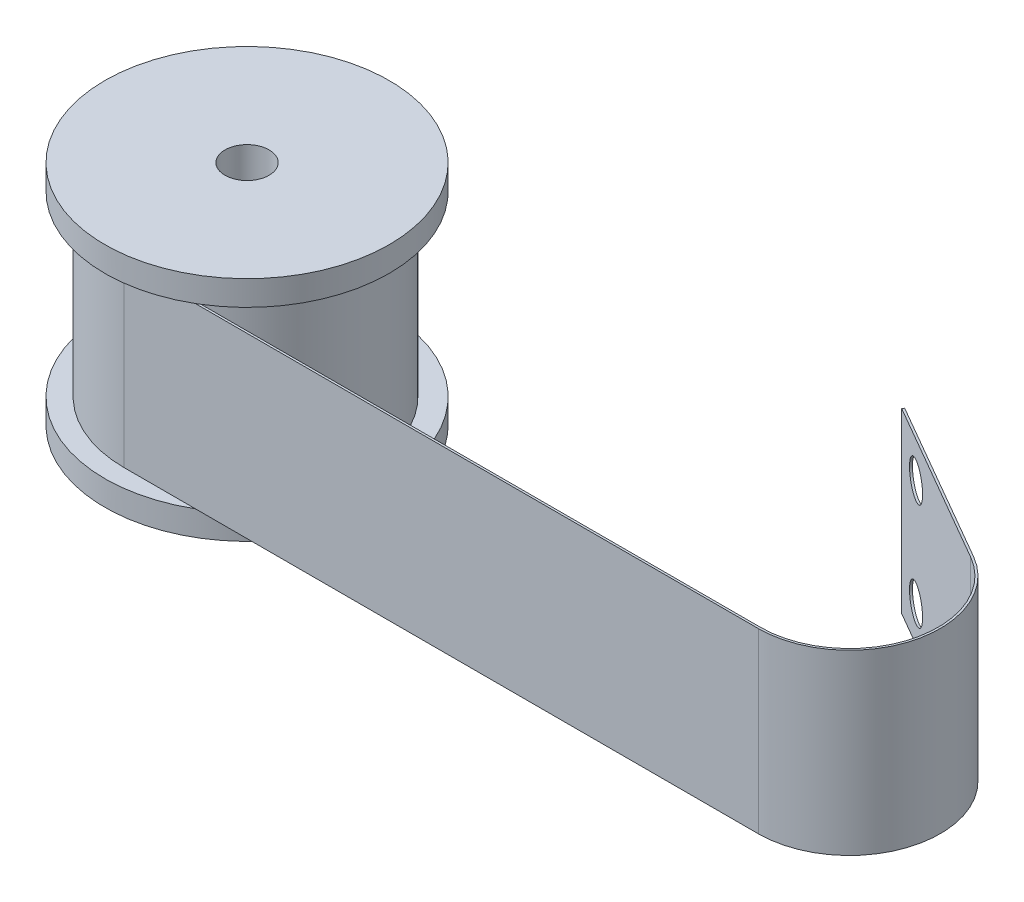
SolidWorks part; units mm, degrees
ref_plane "Front Plane" through (0, 0, 0) normal (0, 0, 1) x (1, 0, 0)
ref_plane "Top Plane" through (0, 0, 0) normal (0, 1, 0) x (1, 0, 0)
ref_plane "Right Plane" through (0, 0, 0) normal (1, 0, 0) x (0, 0, -1)
sketch "Sketch1" plane through (0, 0, 0) normal (0, 0, 1) x (1, 0, 0)
  line L0 (0, -1363.7477) -> (0, 66823.6351) construction
  line L1 (0, 16) -> (3.1, 16) construction
  line L2 (3.1, 0) -> (0, 0) construction
  line L3 (3.1, 16) -> (3.1, -16)
  line L4 (3.1, 0) -> (17, 0) construction
  line L5 (17, -12.5) -> (17, 12.5)
  line L6 (17, 12.5) -> (20, 12.5)
  line L7 (20, 12.5) -> (20, 16)
  line L8 (20, 16) -> (3.1, 16)
  line L9 (20, -12.5) -> (20, -16)
  line L10 (20, -16) -> (3.1, -16)
  line L11 (17, -12.5) -> (20, -12.5)
  dimension "D1" = 40
  dimension "D2" = 6.2
  dimension "D3" = 25
  dimension "D4" = 32
  dimension "D5" = 3
revolve "Revolve1" add sketch "Sketch1" angle 360 about L0
ref_plane "Plane1" through (0, 0, 17) normal (0, 0, 1) x (1, 0, 0)
sketch "Sketch2" plane through (0, -12.5, 0) normal (0, 1, 0) x (1, 0, 0)
  line L0 (0, -17) -> (89.2, -17)
  line L1 (95.45, 6.3253) -> (72.5003, 19.5753)
  line L2 (0, 17) -> (0, -17) construction
  circle A0 centre (0, 0) radius 17 construction
  arc A1 (89.2, -17) -> (95.45, 6.3253) centre (89.2, -4.5) ccw
  arc A2 (0, -17) -> (0, 17) centre (0, 0) cw
  point P6 (0, 0)
  dimension "D1" = 12.5
  dimension "D2" = 89.2
  dimension "D3" = 26.5
  dimension "D4" = 30
extrude "Extrude-Thin2" add sketch "Sketch2" along normal up to surface (25 mm away) thin
sketch "Sketch4" plane through (26.7514, 0, -46.3349) normal (0.5, 0, -0.866) x (-0.866, 0, -0.5)
  line L0 (-58.4995, 12.5) -> (-58.4995, -12.5) construction
  line L1 (-52.9995, 12.5) -> (-79.4995, 12.5) construction
  line L2 (-79.4995, -12.5) -> (-52.9995, -12.5) construction
  line L3 (-58.4995, 7.5) -> (-52.9995, 0) construction
  line L4 (-52.9995, 12.5) -> (-52.9995, -12.5) construction
  line L5 (-52.9995, 0) -> (-58.4995, -7.5) construction
  circle A0 centre (-58.4995, -7.5) radius 2.5
  circle A1 centre (-58.4995, 7.5) radius 2.5
  dimension "D1" = 5
  dimension "D3" = 15
  dimension "D2" = 3
extrude "Cut-Extrude1" cut sketch "Sketch4" against normal up to surface (0.3 mm away) up to face at (83.9752, 0, -12.9503)
